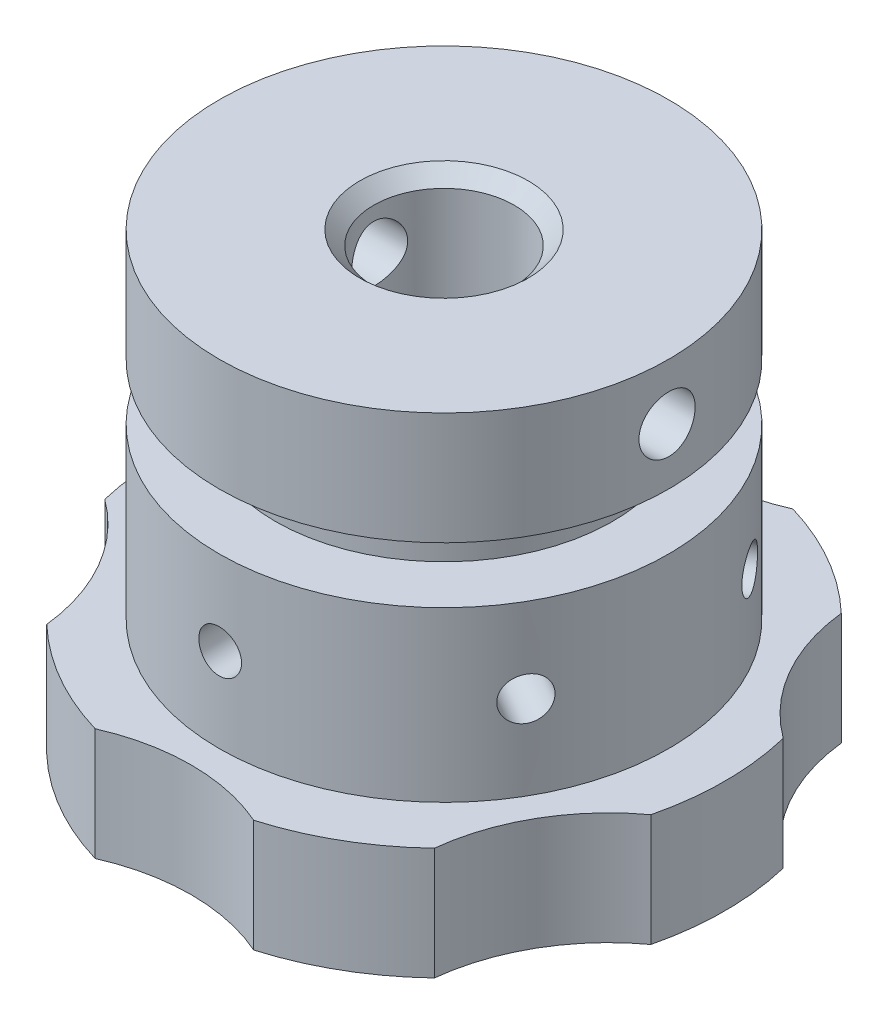
SolidWorks part; units mm, degrees
material "Cast Carbon Steel"
ref_plane "Front Plane" through (0, 0, 0) normal (0, 0, 1) x (1, 0, 0)
ref_plane "Top Plane" through (0, 0, 0) normal (0, 1, 0) x (1, 0, 0)
ref_plane "Right Plane" through (0, 0, 0) normal (1, 0, 0) x (0, 0, -1)
sketch "Sketch1" plane through (0, 0, 0) normal (0, 0, 1) x (1, 0, 0)
  line L0 (0, 0) -> (0, -101.6) construction
  line L1 (0, 0) -> (50.8, 0)
  line L2 (50.8, 0) -> (50.8, -25.4)
  line L3 (50.8, -25.4) -> (38.1, -25.4)
  line L4 (38.1, -25.4) -> (38.1, -38.1)
  line L5 (38.1, -38.1) -> (50.8, -38.1)
  line L6 (50.8, -38.1) -> (50.8, -76.2)
  line L7 (50.8, -76.2) -> (63.5, -76.2)
  line L8 (63.5, -76.2) -> (63.5, -101.6)
  line L9 (63.5, -101.6) -> (0, -101.6)
  line L10 (0, 0) -> (0, -101.6)
  point P7 (50.8, -57.15)
  dimension "D1" = 101.6
  dimension "D2" = 76.2
  dimension "D3" = 63.5
  dimension "D4" = 44.45
  dimension "D5" = 50.8
  dimension "D6" = 63.5
  dimension "D7" = 50.8
  dimension "D8" = 38.1
revolve "Revolve1" add sketch "Sketch1" angle 360 about L0
sketch "Sketch2" plane through (0, -101.6, 0) normal (0, -1, 0) x (1, 0, 0)
  line L0 (0, 84.6856) -> (0, -68.187) construction
  arc A0 (-17.9155, 60.9203) -> (17.9155, 60.9203) centre (0, 101.6) ccw
  circle A1 centre (0, 0) radius 63.5 construction
  arc A2 (-43.8008, 45.9754) -> (-61.7163, 14.9449) centre (0, 0) ccw
  arc A3 (43.8008, 45.9754) -> (61.7163, 14.9449) centre (87.9882, 50.8) ccw
  arc A4 (61.7163, -14.9449) -> (43.8008, -45.9754) centre (87.9882, -50.8) ccw
  arc A5 (17.9155, -60.9203) -> (-17.9155, -60.9203) centre (0, -101.6) ccw
  arc A6 (-43.8008, -45.9754) -> (-61.7163, -14.9449) centre (-87.9882, -50.8) ccw
  arc A7 (-61.7163, 14.9449) -> (-43.8008, 45.9754) centre (-87.9882, 50.8) ccw
  arc A8 (-61.7163, -14.9449) -> (-43.8008, -45.9754) centre (0, 0) ccw
  arc A9 (-17.9155, -60.9203) -> (17.9155, -60.9203) centre (0, 0) ccw
  arc A10 (43.8008, -45.9754) -> (61.7163, -14.9449) centre (0, 0) ccw
  arc A11 (61.7163, 14.9449) -> (43.8008, 45.9754) centre (0, 0) ccw
  arc A12 (17.9155, 60.9203) -> (-17.9155, 60.9203) centre (0, 0) ccw
  point P29 (0, 0)
  dimension "D1" = 44.45
  dimension "D2" = 101.6
  dimension "D4" = 6
extrude "Cut-Extrude1" cut sketch "Sketch2" against normal up to next contours A2 A7 | A6 A8 | A5 A9 | A4 A10 | A3 A11 | A0 A12
sketch "Sketch3" plane through (0, 0, 0) normal (0, 1, 0) x (1, 0, 0)
  circle A0 centre (0, 0) radius 15.875
  dimension "D1" = 31.75
extrude "Cut-Extrude2" cut sketch "Sketch3" against normal up to next
chamfer "Chamfer1" distance 3.175 angle 45 1 edges at (0, 0, 15.875)
sketch "Sketch4" plane through (0, 0, 0) normal (1, 0, 0) x (0, 0, -1)
  line L0 (0, 0) -> (0, -25.4) construction
  line L1 (19.05, 0) -> (-19.05, 0) construction
  line L2 (-38.1, -25.4) -> (38.1, -25.4) construction
  circle A0 centre (0, -12.7) radius 6.35
  dimension "D1" = 12.7
extrude "Cut-Extrude3" cut sketch "Sketch4" against normal mid plane 101.6 contours A0
sketch "Sketch5" plane through (0, 0, 0) normal (0, 0, 1) x (1, 0, 0)
  line L0 (0, 0) -> (0, -101.6) construction
  line L1 (-17.9155, -101.6) -> (17.9155, -101.6) construction
  line L2 (-50.8, -57.15) -> (50.8, -57.15) construction
  line L3 (-50.8, -38.1) -> (-50.8, -76.2) construction
  line L4 (50.8, -76.2) -> (50.8, -38.1) construction
  circle A1 centre (0, -57.15) radius 4.826
  dimension "D1" = 9.652
extrude "Cut-Extrude4" cut sketch "Sketch5" against normal mid plane 101.6
pattern_circular "CirPattern1" count 6 over 360 about axis through (0, -38.1, 0) along (0, 1, 0) of "Cut-Extrude4"
